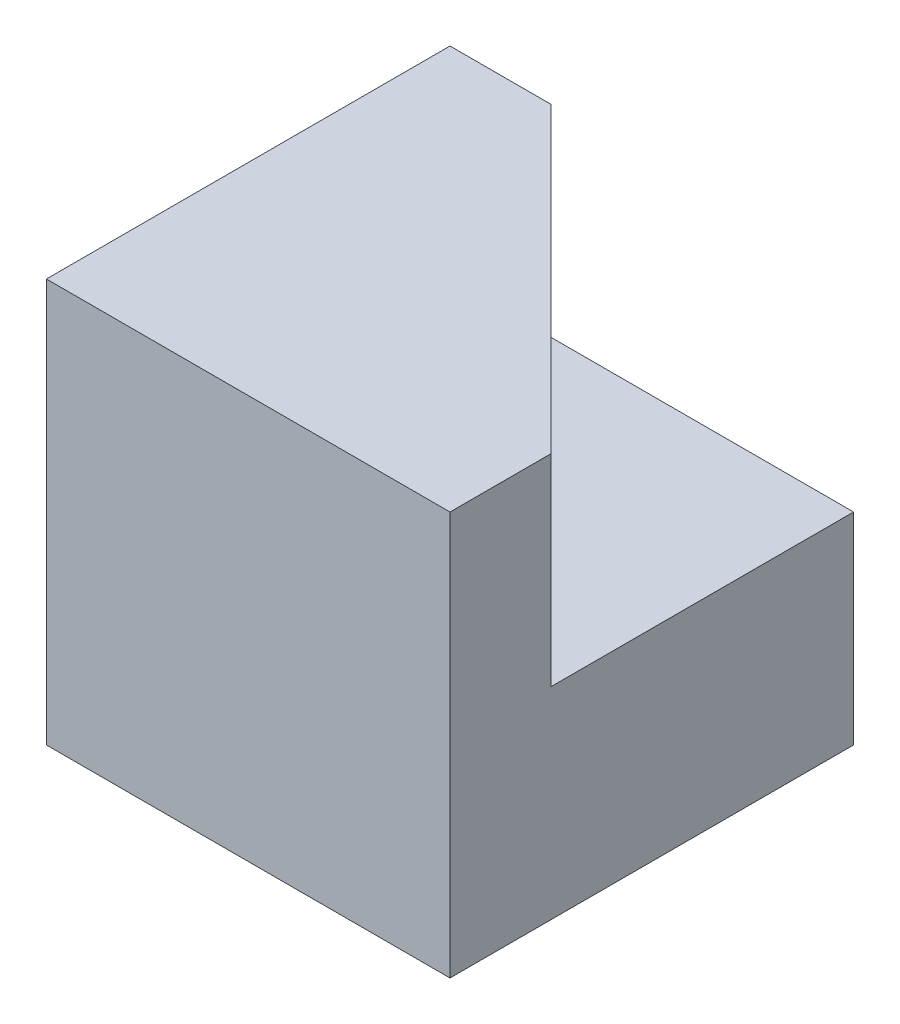
SolidWorks part; units mm, degrees
ref_plane "Front Plane" through (0, 0, 0) normal (0, 0, 1) x (1, 0, 0)
ref_plane "Top Plane" through (0, 0, 0) normal (0, 1, 0) x (1, 0, 0)
ref_plane "Right Plane" through (0, 0, 0) normal (1, 0, 0) x (0, 0, -1)
sketch "Sketch1" plane through (0, 0, 0) normal (0, 0, 1) x (1, 0, 0)
  line L1 (0, 0) -> (40, 0)
  line L2 (0, 0) -> (0, 40)
  line L3 (0, 40) -> (40, 40)
  line L4 (40, 0) -> (40, 40)
  dimension "D1" = 40
  dimension "D2" = 40
extrude "Boss-Extrude1" add sketch "Sketch1" along normal blind 40
sketch "Sketch2" plane through (0, 40, 0) normal (0, 1, 0) x (1, 0, 0)
  line L0 (10, 0) -> (40, -30)
  line L1 (40, 0) -> (0, 0) construction
  line L2 (40, -40) -> (40, 0) construction
  line L3 (40, -30) -> (40, 0)
  line L4 (40, 0) -> (10, 0)
  dimension "D1" = 30
  dimension "D2" = 30
extrude "Cut-Extrude1" cut sketch "Sketch2" against normal blind 20
